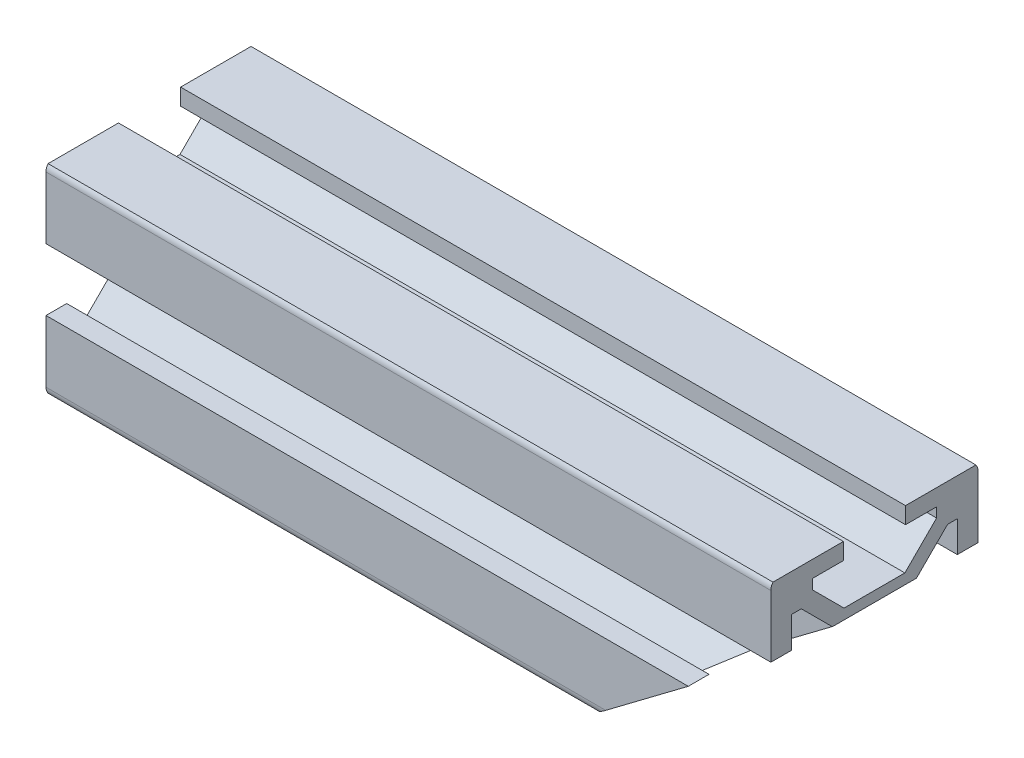
SolidWorks part; units mm, degrees
ref_plane "Front Plane" through (0, 0, 0) normal (0, 0, 1) x (1, 0, 0)
ref_plane "Top Plane" through (0, 0, 0) normal (0, 1, 0) x (1, 0, 0)
ref_plane "Right Plane" through (0, 0, 0) normal (1, 0, 0) x (0, 0, -1)
sketch "Sketch1" plane through (0, 0, 0) normal (1, 0, 0) x (0, 0, -1)
  line L0 (-10, 9) -> (-10, 3)
  line L1 (-10, 3) -> (-8, 3)
  line L2 (-8, 3) -> (-8, 6)
  line L3 (-8, 6) -> (-7.0607, 6)
  line L4 (-7.0607, 6) -> (-4, 2.9393)
  line L5 (-4, 2.9393) -> (-4, -2.9393)
  line L9 (-4, -2.9393) -> (-7.0607, -6)
  line L10 (-7.0607, -6) -> (-8, -6)
  line L11 (-8, -6) -> (-8, -3)
  line L12 (-8, -3) -> (-10, -3)
  line L13 (-10, -3) -> (-10, -9)
  line L14 (-9.8, -9.6) -> (-3, -9.6)
  line L15 (-3, -9.6) -> (-3, -8)
  line L16 (-3, -8) -> (-6, -8)
  line L17 (-6, -8) -> (-6, -7.0607)
  line L18 (-6, -7.0607) -> (-2.9393, -4)
  line L19 (-2.9393, -4) -> (2.9393, -4)
  line L23 (2.9393, -4) -> (6, -7.0607)
  line L24 (6, -7.0607) -> (6, -8)
  line L25 (6, -8) -> (3, -8)
  line L26 (3, -8) -> (3, -9.6)
  line L27 (3, -9.6) -> (9.8, -9.6)
  line L28 (10, -9) -> (10, -3)
  line L29 (10, -3) -> (8, -3)
  line L30 (8, -3) -> (8, -6)
  line L31 (8, -6) -> (7.0607, -6)
  line L32 (7.0607, -6) -> (4, -2.9393)
  line L36 (4, -2.9393) -> (4, 2.9393)
  line L37 (4, 2.9393) -> (7.0607, 6)
  line L38 (7.0607, 6) -> (8, 6)
  line L39 (8, 6) -> (8, 3)
  line L40 (8, 3) -> (10, 3)
  line L41 (10, 3) -> (10, 9)
  line L42 (9.8, 9.6) -> (3, 9.6)
  line L43 (3, 9.6) -> (3, 8)
  line L44 (3, 8) -> (6, 8)
  line L45 (6, 8) -> (6, 7.0607)
  line L46 (6, 7.0607) -> (2.9393, 4)
  line L50 (2.9393, 4) -> (-2.9393, 4)
  line L51 (-2.9393, 4) -> (-6, 7.0607)
  line L52 (-6, 7.0607) -> (-6, 8)
  line L53 (-6, 8) -> (-3, 8)
  line L54 (-3, 8) -> (-3, 9.6)
  line L55 (-3, 9.6) -> (-9.8, 9.6)
  circle A0 centre (0, 0) radius 2.1
  arc A1 (-10, -9) -> (-9.8, -9.6) centre (-9, -9) ccw
  arc A2 (9.8, -9.6) -> (10, -9) centre (9, -9) ccw
  arc A3 (10, 9) -> (9.8, 9.6) centre (9, 9) ccw
  arc A4 (-9.8, 9.6) -> (-10, 9) centre (-9, 9) ccw
  dimension "A" = 20
  dimension "T" = 19.2
extrude "Boss-Extrude1" add sketch "Sketch1" along normal blind 70
ref_plane "Plane1" through (0, 9.6, 0) normal (0, 1, 0) x (1, 0, 0)
ref_plane "Plane2" through (0, 0, 0) normal (1, 0, 0) x (0, 0, -1)
ref_plane "Plane3" through (70, 0, 0) normal (1, 0, 0) x (0, 0, -1)
sketch "Sketch2" [suppressed] plane through (0, 0, 0) normal (0, 0, 1) x (1, 0, 0)
  line L0 (7, -9.6) -> (9.75, -9.6)
  line L1 (9.75, -9.6) -> (9.75, 4)
  line L2 (9.75, 4) -> (11.75, 4)
  line L3 (11.75, 4) -> (11.75, 9.6)
  line L4 (11.75, 9.6) -> (7, 9.6)
  line L5 (7, 9.6) -> (7, -9.6) construction
  line L6 (7, 9.6) -> (7, -9.6)
  point P7 (7, 0)
  dimension "T" = 19.2
  dimension "D1_s" = 9.5
  dimension "D_s" = 5.5
  dimension "FIX_3" = 5.6
  dimension "XA" = 7
revolve "Cut-Revolve1" [suppressed] cut sketch "Sketch2" angle 360 about L5
sketch "Sketch3" [suppressed] plane through (0, 0, 0) normal (0, 0, 1) x (1, 0, 0)
  line L0 (18.5, 9.6) -> (18.5, -9.6) construction
  line L1 (18.5, -9.6) -> (21.25, -9.6)
  line L2 (21.25, -9.6) -> (21.25, 4)
  line L3 (21.25, 4) -> (23.25, 4)
  line L4 (23.25, 4) -> (23.25, 9.6)
  line L5 (23.25, 9.6) -> (18.5, 9.6)
  line L7 (18.5, 9.6) -> (18.5, -9.6)
  point P6 (18.5, 0)
  dimension "D1_s" = 9.5
  dimension "D_s" = 5.5
  dimension "T" = 19.2
  dimension "FIX_5" = 5.6
  dimension "XB" = 19
revolve "Cut-Revolve2" [suppressed] cut sketch "Sketch3" angle 360 about L0
sketch "Sketch4" [suppressed] plane through (0, 0, 0) normal (0, 0, 1) x (1, 0, 0)
  line L0 (30, 9.6) -> (30, -9.6) construction
  line L1 (30, -9.6) -> (32.75, -9.6)
  line L2 (32.75, -9.6) -> (32.75, 4)
  line L3 (32.75, 4) -> (34.75, 4)
  line L4 (34.75, 4) -> (34.75, 9.6)
  line L5 (34.75, 9.6) -> (30, 9.6)
  line L6 (30, 9.6) -> (30, -9.6)
  point P2 (30, 0)
  dimension "D1_s" = 9.5
  dimension "D_s" = 5.5
  dimension "T" = 19.2
  dimension "FIX_7" = 5.6
  dimension "XC" = 31
revolve "Cut-Revolve3" [suppressed] cut sketch "Sketch4" angle 360 about L0
sketch "Sketch5" [suppressed] plane through (0, 0, 0) normal (0, 0, 1) x (1, 0, 0)
  line L0 (41.5, 9.6) -> (41.5, -9.6) construction
  line L1 (41.5, -9.6) -> (44.25, -9.6)
  line L2 (44.25, -9.6) -> (44.25, 4)
  line L3 (44.25, 4) -> (46.25, 4)
  line L4 (46.25, 4) -> (46.25, 9.6)
  line L5 (46.25, 9.6) -> (41.5, 9.6)
  line L7 (41.5, 9.6) -> (41.5, -9.6)
  point P6 (41.5, 0)
  dimension "D1_s" = 9.5
  dimension "D_s" = 5.5
  dimension "FIX_9" = 5.6
  dimension "T" = 19.2
  dimension "XD" = 43
revolve "Cut-Revolve4" [suppressed] cut sketch "Sketch5" angle 360 about L0
sketch "Sketch6" [suppressed] plane through (0, 0, 0) normal (0, 0, 1) x (1, 0, 0)
  line L0 (53, 9.6) -> (53, -9.6) construction
  line L1 (53, -9.6) -> (55.75, -9.6)
  line L2 (55.75, -9.6) -> (55.75, 4)
  line L3 (55.75, 4) -> (57.75, 4)
  line L4 (57.75, 4) -> (57.75, 9.6)
  line L5 (57.75, 9.6) -> (53, 9.6)
  line L6 (53, 9.6) -> (53, -9.6)
  point P6 (53, 0)
  dimension "XE" = 55
  dimension "D1_s" = 9.5
  dimension "D_s" = 5.5
  dimension "T" = 19.2
  dimension "FIX_11" = 5.6
revolve "Cut-Revolve5" [suppressed] cut sketch "Sketch6" angle 360 about L0
sketch "Sketch7" [suppressed] plane through (0, 9.6, 0) normal (0, 1, 0) x (1, 0, 0)
  circle A0 centre (7, 0) radius 3.675
  dimension "D" = 7.35
  dimension "AV" = 7
extrude "Cut-Extrude1" [suppressed] cut sketch "Sketch7" against normal blind 19.2
sketch "Sketch8" [suppressed] plane through (0, 9.6, 0) normal (0, 1, 0) x (1, 0, 0)
  circle A0 centre (18.5, 0) radius 3.675
  dimension "D" = 7.35
  dimension "BV" = 19
extrude "Cut-Extrude2" [suppressed] cut sketch "Sketch8" against normal blind 19.2
sketch "Sketch9" [suppressed] plane through (0, 9.6, 0) normal (0, 1, 0) x (1, 0, 0)
  circle A0 centre (30, 0) radius 3.675
  dimension "D" = 7.35
  dimension "CV" = 31
extrude "Cut-Extrude3" [suppressed] cut sketch "Sketch9" against normal blind 19.2
sketch "Sketch10" [suppressed] plane through (0, 9.6, 0) normal (0, 1, 0) x (1, 0, 0)
  circle A0 centre (41.5, 0) radius 3.675
  dimension "D" = 7.35
  dimension "DV" = 43
extrude "Cut-Extrude4" [suppressed] cut sketch "Sketch10" against normal blind 19.2
sketch "Sketch11" [suppressed] plane through (0, 9.6, 0) normal (0, 1, 0) x (1, 0, 0)
  circle A0 centre (53, 0) radius 3.675
  dimension "D" = 7.35
  dimension "EV" = 55
extrude "Cut-Extrude5" [suppressed] cut sketch "Sketch11" against normal blind 19.2
sketch "Sketch12" [suppressed] plane through (0, 0, 0) normal (1, 0, 0) x (0, 0, -1)
  circle A0 centre (0, 0) radius 2.1
  dimension "FIX_13" = 4.2
extrude "Boss-Extrude2" [suppressed] add sketch "Sketch12" along normal blind 15
hole_wizard "Tapped Hole1" [suppressed] positions "Sketch14" profile "Sketch13" tap size "M5x0.8" standard "JIS"
sketch "Sketch14" [suppressed] plane through (0, 0, 0) normal (1, 0, 0) x (0, 0, -1)
  point P0 (0, 0)
sketch "Sketch13" [suppressed] plane through (0, 0, 0) normal (0, 1, 0) x (0, 0, 1)
  line L0 (0, 0) -> (0, 15)
  line L1 (0, 15) -> (2.1, 15)
  line L2 (2.1, 15) -> (2.1, 0)
  line L5 (2.1, 0) -> (0, 0)
  line L11 (0, -6.35) -> (0, 107.95) construction
  dimension "Thru Tap Drill Dia." = 4.2
  dimension "Thru Tap Drill Depth" = 15
cosmetic thread "Hole Thread1" [suppressed] parameters "NFIX_2"=15, "NFIX_1"=5
sketch "Sketch15" [suppressed] plane through (100, 0, 0) normal (1, 0, 0) x (0, 0, -1)
  circle A0 centre (0, 0) radius 2.1
  dimension "FIX_15" = 4.2
extrude "Boss-Extrude3" [suppressed] add sketch "Sketch15" against normal blind 15
hole_wizard "Tapped Hole2" [suppressed] positions "Sketch17" profile "Sketch16" tap size "M5x0.8" standard "JIS"
sketch "Sketch17" [suppressed] plane through (100, 0, 0) normal (1, 0, 0) x (0, 0, -1)
  point P0 (0, 0)
sketch "Sketch16" [suppressed] plane through (100, 0, 0) normal (0, 1, 0) x (0, 0, -1)
  line L0 (0, 0) -> (0, 15)
  line L1 (0, 15) -> (2.1, 15)
  line L2 (2.1, 15) -> (2.1, 0)
  line L5 (2.1, 0) -> (0, 0)
  line L11 (0, -6.35) -> (0, 107.95) construction
  dimension "Thru Tap Drill Dia." = 4.2
  dimension "Thru Tap Drill Depth" = 15
cosmetic thread "Hole Thread2" [suppressed] parameters "NFIX_2"=15, "NFIX_1"=5
sketch "Sketch18" [suppressed] plane through (0, 0, 0) normal (1, 0, 0) x (0, 0, -1)
  circle A0 centre (0, 0) radius 2.1
  dimension "FIX_17" = 4.2
extrude "Boss-Extrude4" [suppressed] add sketch "Sketch18" along normal blind 15
sketch "Sketch19" [suppressed] plane through (100, 0, 0) normal (1, 0, 0) x (0, 0, -1)
  circle A0 centre (0, 0) radius 2.1
  dimension "FIX_19" = 4.2
extrude "Boss-Extrude5" [suppressed] add sketch "Sketch19" against normal blind 15
hole_wizard "Tapped Hole3" [suppressed] positions "Sketch21" profile "Sketch20" tap size "M5x0.8" standard "JIS"
sketch "Sketch21" [suppressed] plane through (0, 0, 0) normal (1, 0, 0) x (0, 0, -1)
  point P0 (0, 0)
sketch "Sketch20" [suppressed] plane through (0, 0, 0) normal (0, 1, 0) x (0, 0, 1)
  line L0 (0, 0) -> (0, 15)
  line L1 (0, 15) -> (2.1, 15)
  line L2 (2.1, 15) -> (2.1, 0)
  line L5 (2.1, 0) -> (0, 0)
  line L11 (0, -6.35) -> (0, 107.95) construction
  dimension "Thru Tap Drill Dia." = 4.2
  dimension "Thru Tap Drill Depth" = 15
cosmetic thread "Hole Thread3" [suppressed] parameters "NFIX_2"=15, "NFIX_1"=5
hole_wizard "Tapped Hole4" [suppressed] positions "Sketch23" profile "Sketch22" tap size "M5x0.8" standard "JIS"
sketch "Sketch23" [suppressed] plane through (100, 0, 0) normal (1, 0, 0) x (0, 0, -1)
  point P0 (0, 0)
sketch "Sketch22" [suppressed] plane through (100, 0, 0) normal (0, 1, 0) x (0, 0, -1)
  line L0 (0, 0) -> (0, 15)
  line L1 (0, 15) -> (2.1, 15)
  line L2 (2.1, 15) -> (2.1, 0)
  line L5 (2.1, 0) -> (0, 0)
  line L11 (0, -6.35) -> (0, 107.95) construction
  dimension "Thru Tap Drill Dia." = 4.2
  dimension "Thru Tap Drill Depth" = 15
cosmetic thread "Hole Thread4" [suppressed] parameters "NFIX_2"=15, "NFIX_1"=5
sketch "草图1" plane through (0, 0, 10) normal (0, 0, 1) x (1, 0, 0)
  line L0 (53.2522, -9.6) -> (70, 3)
  line L1 (70, -9.6) -> (0, -9.6) construction
  line L2 (70, 3) -> (72.1087, -2.8497)
  line L3 (72.1087, -2.8497) -> (72.521, -11.3881)
  line L4 (72.521, -11.3881) -> (53.2522, -9.6)
extrude "切除-拉伸1" cut sketch "草图1" against normal through all both and the other way through all
